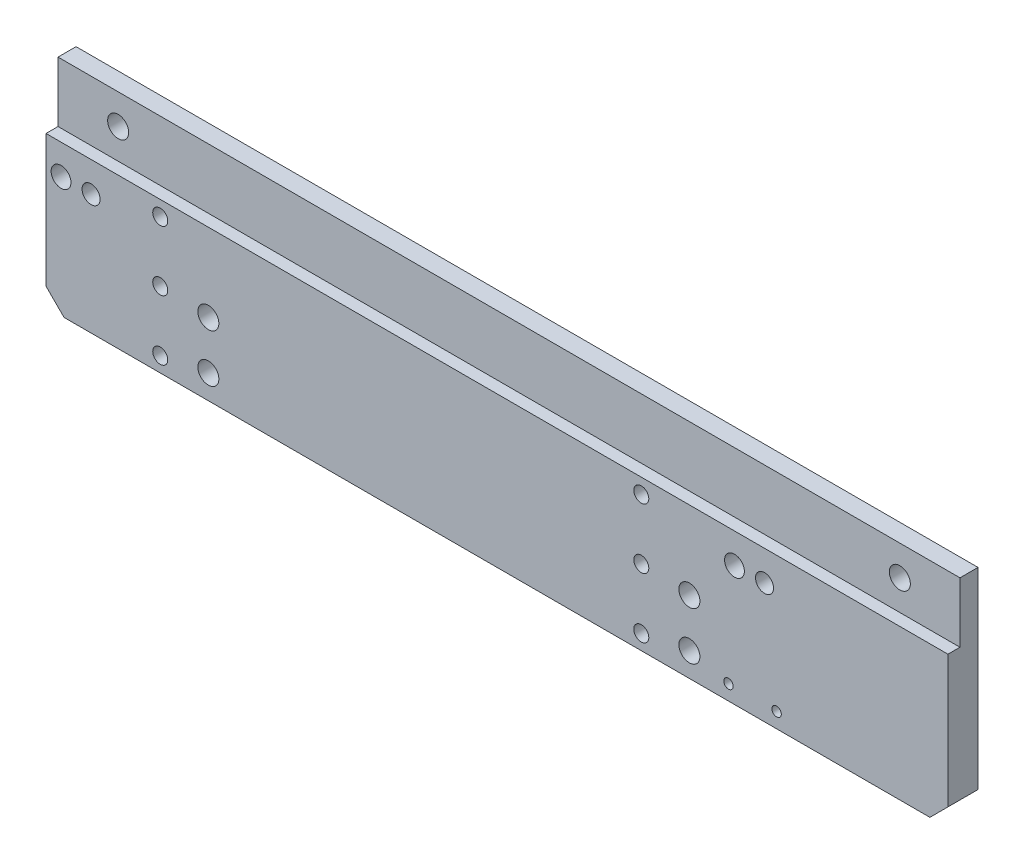
SolidWorks part; units mm, degrees
ref_plane "Front Plane" through (0, 0, 0) normal (0, 0, 1) x (1, 0, 0)
ref_plane "Top Plane" through (0, 0, 0) normal (0, 1, 0) x (1, 0, 0)
ref_plane "Right Plane" through (0, 0, 0) normal (1, 0, 0) x (0, 0, -1)
sketch "Sketch1" plane through (0, 0, 0) normal (0, 0, 1) x (1, 0, 0)
  line L0 (72, -17.5) -> (75, -14.5)
  line L1 (-72, -17.5) -> (72, -17.5)
  line L2 (-75, -14.5) -> (-75, 17.5)
  line L3 (-75, 17.5) -> (75, 17.5)
  line L4 (75, -14.5) -> (75, 17.5)
  line L5 (-75, -17.5) -> (75, 17.5) construction
  line L6 (-75, 17.5) -> (75, -17.5) construction
  line L7 (-75, -14.5) -> (-72, -17.5)
  point P0 (0, 0)
  dimension "D1" = 150
  dimension "D2" = 35
extrude "Boss-Extrude1" add sketch "Sketch1" along normal blind 5
sketch "Sketch2" plane through (75, 0, 0) normal (1, 0, 0) x (0, 0, -1)
  line L0 (-5, -14.5) -> (-5, 17.5) construction
  line L1 (-5, 7.5) -> (-3, 7.5)
  line L2 (-5, 7.5) -> (-5, 17.5)
  line L3 (-5, 17.5) -> (-3, 17.5)
  line L4 (-3, 7.5) -> (-3, 17.5)
  line L5 (-5, 17.5) -> (0, 17.5) construction
  dimension "D1" = 2
  dimension "D2" = 10
extrude "Cut-Extrude1" cut sketch "Sketch2" against normal through all
sketch "Sketch3" plane through (0, 0, 0) normal (0, 0, -1) x (-1, 0, 0)
  line L0 (-75, 17.5) -> (75, 17.5) construction
  line L1 (-75, -14.5) -> (-75, 17.5) construction
  line L2 (72, -17.5) -> (-72, -17.5) construction
  line L3 (75, 17.5) -> (75, -14.5) construction
  circle A0 centre (-65, 12.5) radius 1.75
  circle A1 centre (65, 12.5) radius 1.75
  circle A2 centre (-44.5, 2.5) radius 1.5
  circle A3 centre (-39.5, 2.5) radius 1.65
  circle A4 centre (-46.5, -15) radius 0.785
  circle A5 centre (-38.5, -15) radius 0.785
  circle A6 centre (-32, -5.5) radius 1.75
  circle A7 centre (-32, -13.5) radius 1.75
  circle A8 centre (48, -5.5) radius 1.75
  circle A9 centre (48, -13.5) radius 1.75
  circle A10 centre (67.5, 2.5) radius 1.5
  circle A11 centre (72.5, 2.5) radius 1.65
  dimension "D1" = 5
  dimension "D2" = 10
  dimension "D3" = 3.5
  dimension "D4" = 130
  dimension "D5" = 1.57
  dimension "D7" = 2.5
  dimension "D9" = 3
  dimension "D10" = 3.3
  dimension "D11" = 15
  dimension "D13" = 3.5
  dimension "D17" = 5
  dimension "D18" = 15
  dimension "D19" = 4
  dimension "D20" = 2.5
  dimension "D21" = 28.5
  dimension "D6" = 8
  dimension "D8" = 5
  dimension "D12" = 30.5
  dimension "D14" = 8
  dimension "D15" = 80
  dimension "D16" = 27
extrude "Cut-Extrude2" cut sketch "Sketch3" against normal through all
sketch "Sketch4" plane through (0, 0, 0) normal (0, 0, -1) x (-1, 0, 0)
  line L1 (-75, 17.5) -> (75, 17.5) construction
  line L2 (-75, -14.5) -> (-75, 17.5) construction
  circle A0 centre (-24, 5) radius 2
  dimension "D1" = 4
  dimension "D2" = 12.5
  dimension "D3" = 51
extrude "Cut-Extrude3" cut sketch "Sketch4" against normal blind 2.5
sketch "Sketch5" plane through (0, 0, 2.5) normal (0, 0, -1) x (-1, 0, 0)
  circle A0 centre (-24, 5) radius 1.25
  dimension "D1" = 2.5
extrude "Cut-Extrude4" cut sketch "Sketch5" against normal through all
pattern_linear "LPattern1" count 3 spacing 10 along (0, -1, 0) count 2 spacing 80 along (-1, 0, 0) of "Cut-Extrude3", "Cut-Extrude4"
